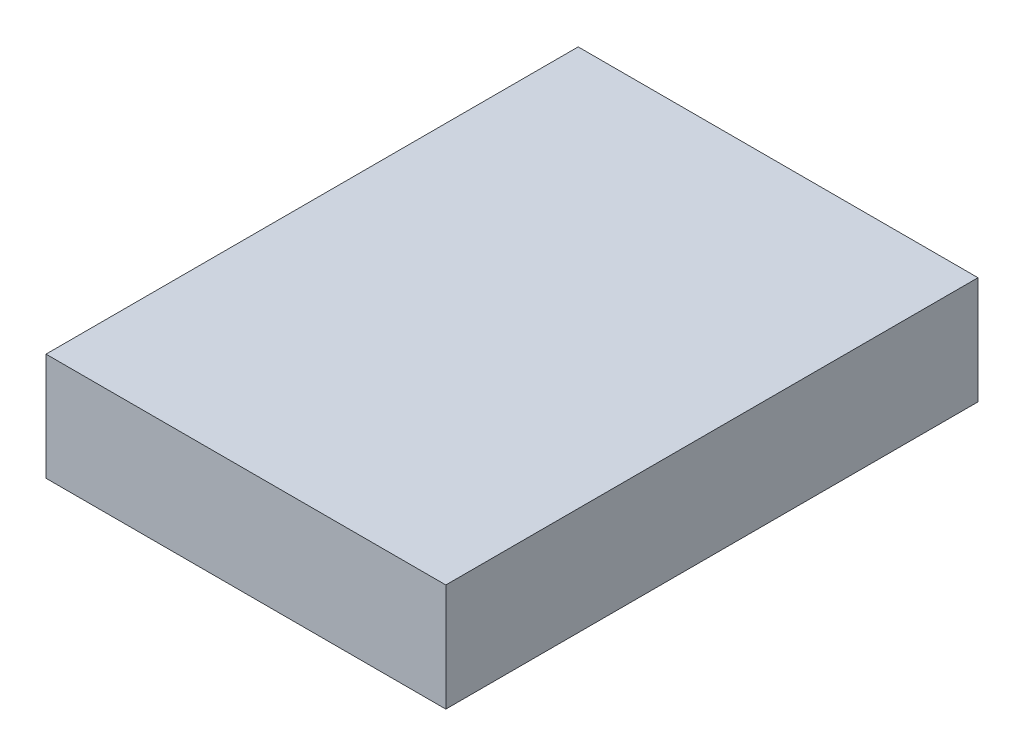
SolidWorks part; units mm, degrees
ref_plane "Front" through (0, 0, 0) normal (0, 0, 1) x (1, 0, 0)
ref_plane "Top" through (0, 0, 0) normal (0, 1, 0) x (1, 0, 0)
ref_plane "Right" through (0, 0, 0) normal (1, 0, 0) x (0, 0, -1)
sketch "Sketch1" plane through (0, 0, 0) normal (0, 1, 0) x (1, 0, 0)
  line L1 (0, 0) -> (72.5, 0)
  line L2 (0, 0) -> (0, 96.5)
  line L3 (0, 96.5) -> (72.5, 96.5)
  line L4 (72.5, 0) -> (72.5, 96.5)
  dimension "D1" = 96.5
  dimension "D2" = 72.5
extrude "Boss-Extrude1" add sketch "Sketch1" along normal blind 19.5
